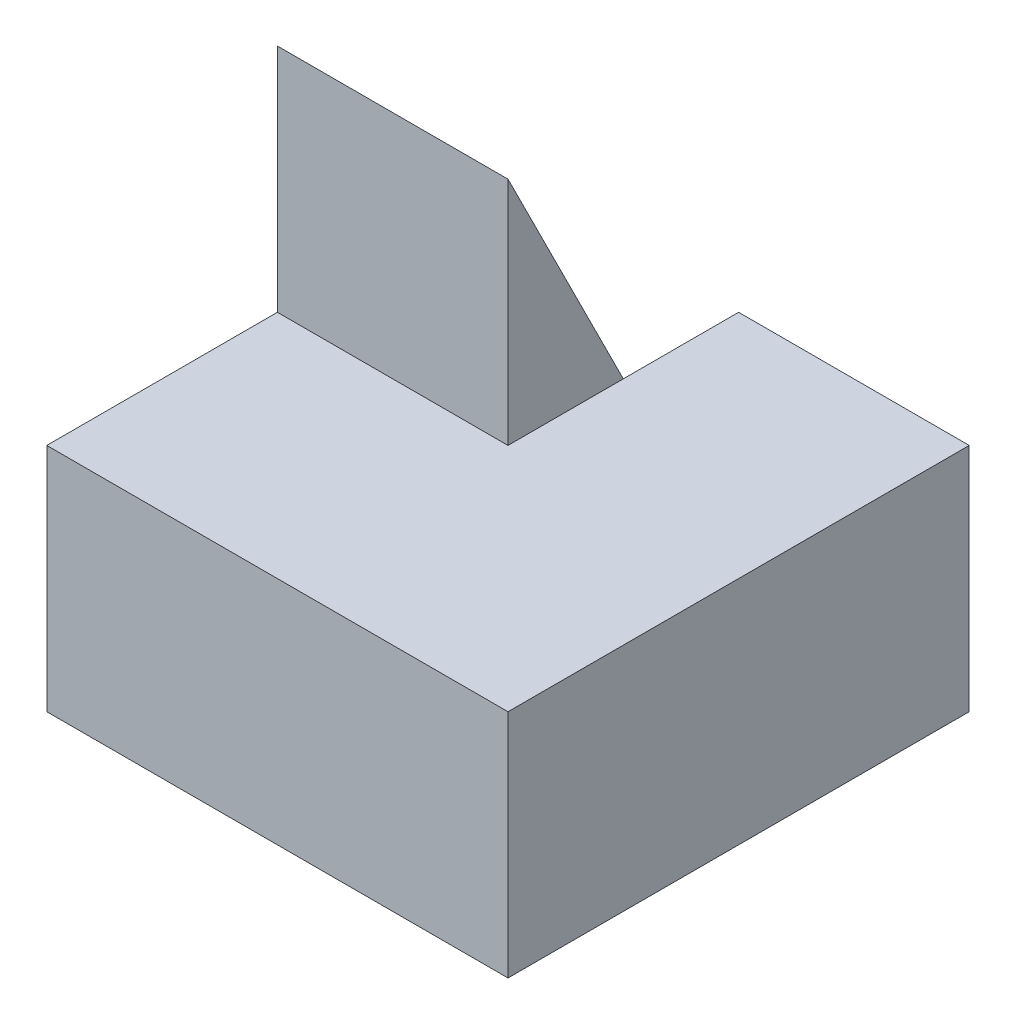
SolidWorks part; units mm, degrees
ref_plane "Front" through (0, 0, 0) normal (0, 0, 1) x (1, 0, 0)
ref_plane "Top" through (0, 0, 0) normal (0, 1, 0) x (1, 0, 0)
ref_plane "Right" through (0, 0, 0) normal (1, 0, 0) x (0, 0, -1)
sketch "Sketch1" plane through (0, 0, 0) normal (0, 1, 0) x (1, 0, 0)
  line L1 (0, 0) -> (4, 0)
  line L2 (0, 0) -> (0, 4)
  line L3 (0, 4) -> (4, 4)
  line L4 (4, 0) -> (4, 4)
  dimension "D1" = 4
  dimension "D2" = 4
extrude "Boss-Extrude1" add sketch "Sketch1" along normal blind 4
sketch "Sketch2" plane through (0, 4, 0) normal (0, 1, 0) x (1, 0, 0)
  line L5 (0, 4) -> (2, 4)
  line L6 (0, 4) -> (0, 2)
  line L7 (0, 2) -> (2, 2)
  line L8 (2, 4) -> (2, 2)
  line M1 (0, 4) -> (0, 0)
  line M2 (0, 0) -> (4, 0)
  line M3 (4, 0) -> (4, 4)
  line M4 (4, 4) -> (0, 4)
  dimension "D1" = 2
  dimension "D2" = 2
extrude "Cut-Extrude1" cut sketch "Sketch2" against normal blind 2 contours L8 L7 M4 M1 M2 M3
sketch "Sketch3" plane through (0, 0, 0) normal (-1, 0, 0) x (0, 0, 1)
  line L0 (-2, 4) -> (-4, 0)
  line L1 (-4, 0) -> (-4, 4)
  line L2 (-4, 4) -> (-2, 4)
extrude "Cut-Extrude2" cut sketch "Sketch3" against normal blind 2
